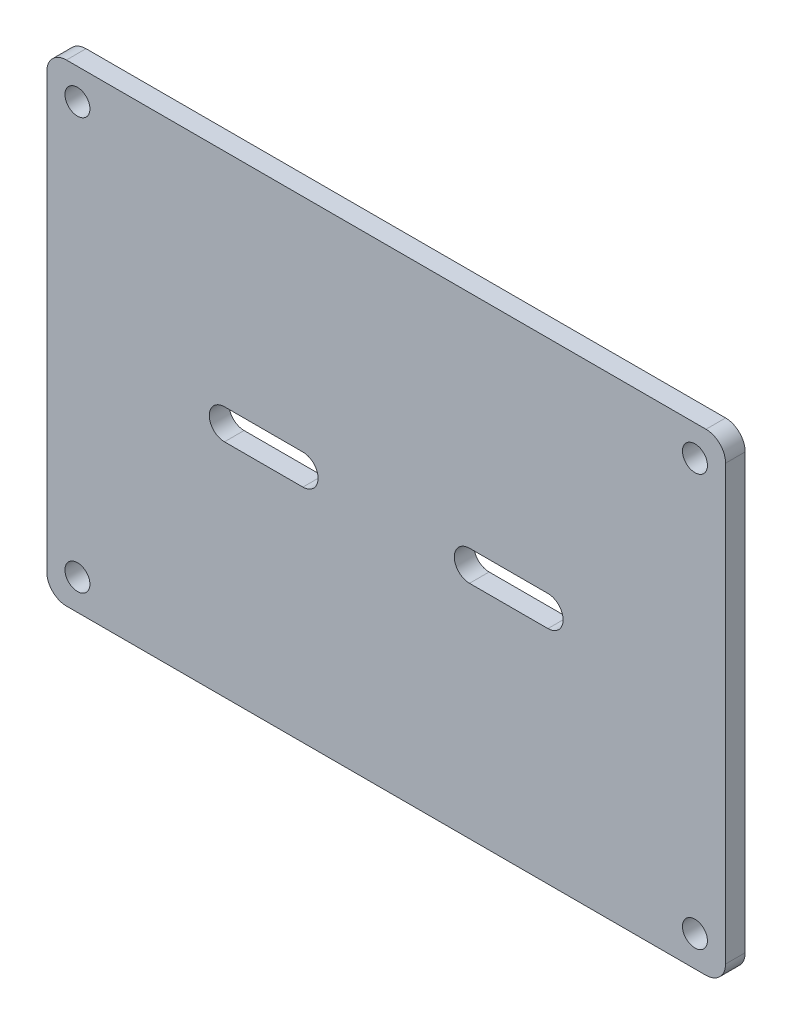
SolidWorks part; units mm, degrees
ref_plane "前视基准面" through (0, 0, 0) normal (0, 0, 1) x (1, 0, 0)
ref_plane "上视基准面" through (0, 0, 0) normal (0, 1, 0) x (1, 0, 0)
ref_plane "右视基准面" through (0, 0, 0) normal (1, 0, 0) x (0, 0, -1)
other "Configuration Table"
sketch "草图1" plane through (0, 0, 0) normal (0, 0, 1) x (1, 0, 0)
  line L0 (0, 0) -> (50000, 0) construction
  line L1 (-31.5, -21) -> (31.5, -21) construction
  line L2 (-31.5, -21) -> (-31.5, 21) construction
  line L3 (-31.5, 21) -> (31.5, 21) construction
  line L4 (31.5, -21) -> (31.5, 21) construction
  line L5 (-31.5, -21) -> (31.5, 21) construction
  line L6 (-31.5, 21) -> (31.5, -21) construction
  line L7 (34.625, -24.125) -> (-34.625, -24.125)
  line L8 (34.625, -24.125) -> (34.625, 24.125)
  line L9 (34.625, 24.125) -> (-34.625, 24.125)
  line L10 (-34.625, -24.125) -> (-34.625, 24.125)
  line L11 (34.625, -24.125) -> (-34.625, 24.125) construction
  line L12 (34.625, 24.125) -> (-34.625, -24.125) construction
  line L13 (-16.5, 0) -> (-8.5, 0) construction
  line L14 (-16.5, 1.55) -> (-8.5, 1.55)
  line L15 (-16.5, -1.55) -> (-8.5, -1.55)
  line L16 (16.5, 0) -> (8.5, 0) construction
  line L17 (16.5, -1.55) -> (8.5, -1.55)
  line L18 (16.5, 1.55) -> (8.5, 1.55)
  line L19 (0, 0) -> (0, -50000) construction
  circle A0 centre (-31.5, 21) radius 3.125 construction
  circle A1 centre (-31.5, 21) radius 1.275
  circle A2 centre (31.5, 21) radius 1.275
  circle A3 centre (-31.5, -21) radius 1.275
  circle A4 centre (31.5, -21) radius 1.275
  arc A5 (-16.5, 1.55) -> (-16.5, -1.55) centre (-16.5, 0) ccw
  arc A6 (-8.5, -1.55) -> (-8.5, 1.55) centre (-8.5, 0) ccw
  arc A7 (16.5, -1.55) -> (16.5, 1.55) centre (16.5, 0) ccw
  arc A8 (8.5, 1.55) -> (8.5, -1.55) centre (8.5, 0) ccw
  point P0 (0, 0)
  point P6 (0, 0)
  point P20 (-12.5, 0)
  point P26 (12.5, 0)
  point P32 (0, 0)
  point P35 (0, 0)
  point P36 (0, 0)
  dimension "D3" = 6.25
  dimension "D4" = 2.55
  dimension "D5" = 1.55
  dimension "D1" = 63
  dimension "D2" = 42
  dimension "D6" = 8
  dimension "D7" = 25
  dimension "D8" = 12.5
extrude "凸台-拉伸1" add sketch "草图1" along normal blind 2
fillet "圆角1" radius 2 4 edges at (-34.625, 24.125, 1) (34.625, -24.125, 1) (-34.625, -24.125, 1) (34.625, 24.125, 1)
